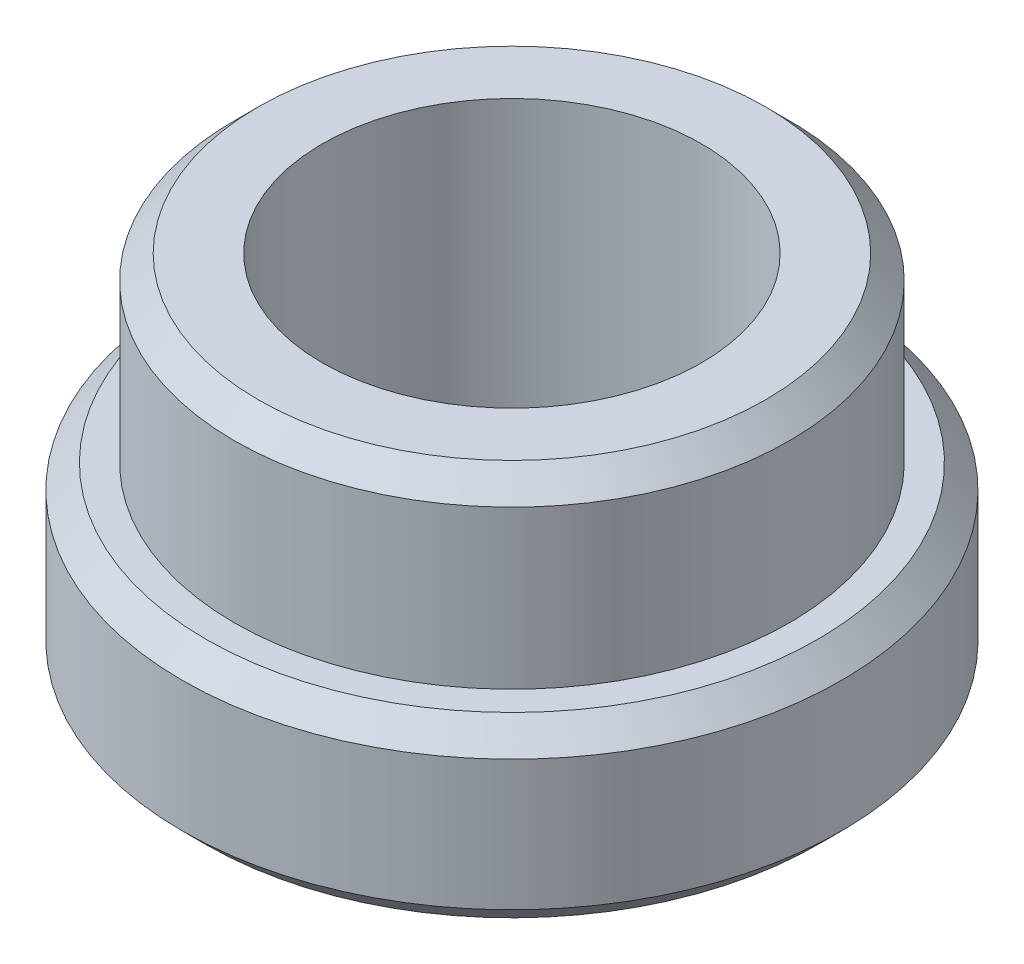
SolidWorks part; units mm, degrees
material "Chrome Stainless Steel"
ref_plane "Front Plane" through (0, 0, 0) normal (0, 0, 1) x (1, 0, 0)
ref_plane "Top Plane" through (0, 0, 0) normal (0, 1, 0) x (1, 0, 0)
ref_plane "Right Plane" through (0, 0, 0) normal (1, 0, 0) x (0, 0, -1)
sketch "Sketch1" plane through (0, 0, 0) normal (0, 1, 0) x (1, 0, 0)
  circle A0 centre (0, 0) radius 2.78
  dimension "D1" = 5.56
extrude "Boss-Extrude1" add sketch "Sketch1" along normal blind 1.5
chamfer "Chamfer1" distance 0.2 angle 45 2 edges at (0, 1.5, 2.78) (0, 0, 2.78)
sketch "Sketch2" plane through (0, 1.5, 0) normal (0, 1, 0) x (1, 0, 0)
  circle A0 centre (0, 0) radius 2.34
  dimension "D1" = 4.68
extrude "Boss-Extrude2" add sketch "Sketch2" along normal blind 1.53
chamfer "Chamfer2" distance 0.2 angle 45 1 edges at (0, 3.03, 2.34)
sketch "Sketch3" plane through (0, 3.03, 0) normal (0, 1, 0) x (1, 0, 0)
  circle A0 centre (0, 0) radius 1.6
  dimension "D1" = 3.2
extrude "Cut-Extrude1" cut sketch "Sketch3" against normal through all
